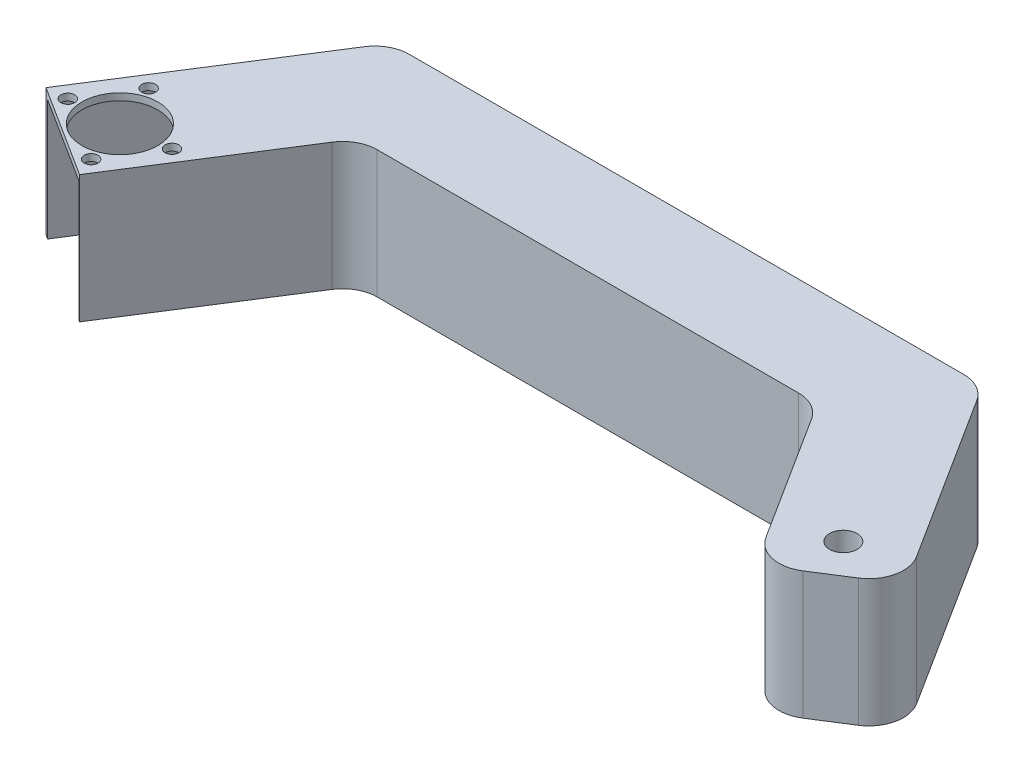
SolidWorks part; units mm, degrees
ref_plane "Front Plane" through (0, 0, 0) normal (0, 0, 1) x (1, 0, 0)
ref_plane "Top Plane" through (0, 0, 0) normal (0, 1, 0) x (1, 0, 0)
ref_plane "Right Plane" through (0, 0, 0) normal (1, 0, 0) x (0, 0, -1)
sketch "Sketch1" plane through (0, 0, 0) normal (0, 1, 0) x (1, 0, 0)
  line L4 (30.9136, -11.507) -> (61.4102, 36.4717)
  line L6 (80.7314, 7.8554) -> (57.6301, -28.4887)
  line L8 (89.1708, 12.4911) -> (211.3631, 12.4911)
  line L9 (69.8496, 41.1074) -> (230.6842, 41.1074)
  line L10 (150.2669, 12.4911) -> (150.2669, 90.3966) construction
  line L11 (256.7076, -31.5638) -> (266.5452, -25.3107)
  line L12 (219.8025, 7.8554) -> (242.9038, -28.4887)
  line L13 (269.6203, -11.507) -> (239.1237, 36.4717)
  line L14 (59.0368, -26.2755) -> (47.8987, -43.7986) construction
  line L15 (30.9136, -11.507) -> (19.9619, -28.7367) construction
  line L16 (38.9075, -28.4373) -> (56.1402, -39.3908) construction
  line L17 (56.1402, -39.3908) -> (15.9099, -13.8193) construction
  line L18 (57.6301, -28.4887) -> (52.2657, -36.9281)
  line L19 (52.2657, -36.9281) -> (25.5493, -19.9464)
  line L20 (25.5493, -19.9464) -> (30.9136, -11.507)
  arc A0 (69.8496, 41.1074) -> (61.4102, 36.4717) centre (69.8496, 31.1074) ccw
  arc A1 (89.1708, 12.4911) -> (80.7314, 7.8554) centre (89.1708, 2.4911) ccw
  arc A4 (269.6203, -11.507) -> (266.5452, -25.3107) centre (261.1808, -16.8713) cw
  arc A5 (256.7076, -31.5638) -> (242.9038, -28.4887) centre (251.3433, -23.1244) cw
  arc A6 (211.3631, 12.4911) -> (219.8025, 7.8554) centre (211.3631, 2.4911) cw
  arc A7 (230.6842, 41.1074) -> (239.1237, 36.4717) centre (230.6842, 31.1074) cw
  point P18 (150.2669, 41.1074)
  dimension "D1" = 10
  dimension "D2" = 10
extrude "Boss-Extrude1" add sketch "Sketch1" along normal blind 37
sketch "Sketch3" plane through (0, 37, 0) normal (0, 1, 0) x (1, 0, 0)
  line L0 (63.7474, -9.8637) -> (54.6281, -24.2107) construction
  line L2 (150.2669, 41.1074) -> (150.2669, -42.4536) construction
  line L3 (230.6842, 41.1074) -> (69.8496, 41.1074) construction
  line L4 (51.7819, -8.1826) -> (38.9075, -28.4373) construction
  line L5 (55.1129, -14.4471) -> (63.2626, -19.6273) construction
  line L6 (45.3447, -18.31) -> (58.7029, -26.8008) construction
  line L7 (52.2657, -36.9281) -> (80.7314, 7.8554) construction
  line L8 (45.3447, -18.31) -> (31.9865, -9.8191) construction
  line L9 (61.4102, 36.4717) -> (25.5493, -19.9464) construction
  line L10 (255.1892, -18.31) -> (268.5474, -9.8191) construction
  line L11 (269.6203, -11.507) -> (239.1237, 36.4717) construction
  line L12 (44.6959, -7.8258) -> (36.5462, -2.6456) construction
  line L13 (25.5493, -19.9464) -> (52.2657, -36.9281) construction
  circle A0 centre (45.3447, -18.31) radius 11
  circle A2 centre (255.1892, -18.31) radius 11 construction
  circle A5 centre (40.621, -5.2357) radius 2
  circle A6 centre (59.1878, -17.0372) radius 2
  circle A7 centre (255.1892, -18.31) radius 4
  circle A8 centre (50.0684, -31.3842) radius 2
  circle A9 centre (31.5017, -19.5827) radius 2
  point P23 (59.1878, -17.0372)
  point P30 (45.3447, -18.31)
  point P32 (59.1878, -17.0372)
  point P36 (40.621, -5.2357)
  dimension "D1" = 12
  dimension "D2" = 11
  dimension "D4" = 8.5
  dimension "D5" = 8.5
  dimension "D3" = 11
ref_plane "Plane1" through (150.265, 0, 0) normal (1, 0, 0) x (0, 0, -1)
extrude "Cut-Extrude1" cut sketch "Sketch3" against normal blind 92
sketch "Sketch9" plane through (0, 0, 0) normal (0, -1, 0) x (1, 0, 0)
  line L2 (40.7081, -1.1059) -> (39.4422, -1.9105) construction
  line L6 (219.8025, -7.8554) -> (242.9038, 28.4887) construction
  line L10 (269.6203, 11.507) -> (239.1237, -36.4717) construction
  line L11 (226.7399, 3.0589) -> (228.4278, 1.986) construction
  line L12 (251.2027, -13.74) -> (252.8906, -14.8129) construction
  line L13 (150.2669, -41.1074) -> (150.265, 31.662) construction
  line L14 (61.4102, -36.4717) -> (25.5493, 19.9464) construction
  line L15 (64.5415, 14.819) -> (65.8075, 15.6236) construction
  line L16 (230.6842, -41.1074) -> (69.8496, -41.1074) construction
  line L17 (52.2657, 36.9281) -> (80.7314, -7.8554) construction
  line L18 (26.2487, 21.6397) -> (55.1675, -23.8515)
  line L19 (51.2146, 37.5106) -> (26.2487, 21.6397)
  line L20 (78.922, -9.6664) -> (51.2146, 37.5106)
  line L21 (55.1675, -23.8515) -> (78.922, -9.6664)
extrude "Cut-Extrude5" cut sketch "Sketch9" against normal blind 35
ref_plane "Plane3" through (81.7227, 0, 128.57) normal (0.5364, 0, 0.8439) x (0.8439, 0, -0.5364)
ref_plane "Plane4" through (4.7592, 0, -7.4873) normal (-0.5364, 0, 0.8439) x (0.8439, 0, 0.5364)
ref_plane "Plane5" through (0, 35, 0) normal (0, -1, 0) x (-1, 0, 0)
